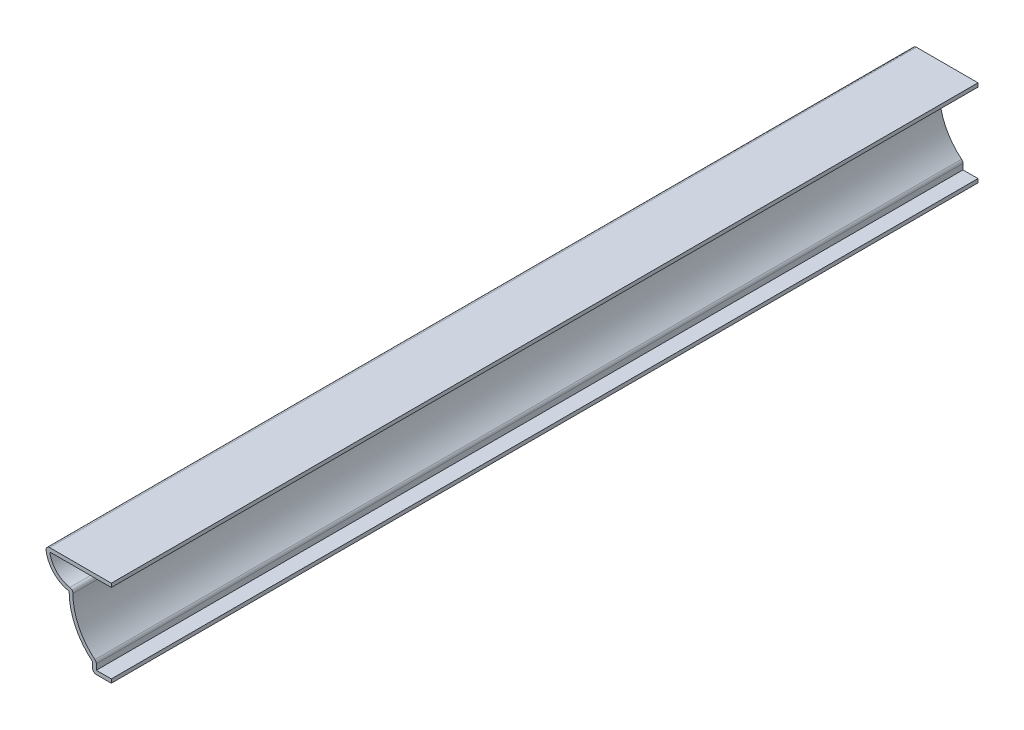
SolidWorks part; units mm, degrees
ref_plane "Front Plane" through (0, 0, 0) normal (0, 0, 1) x (1, 0, 0)
ref_plane "Top Plane" through (0, 0, 0) normal (0, 1, 0) x (1, 0, 0)
ref_plane "Right Plane" through (0, 0, 0) normal (1, 0, 0) x (0, 0, -1)
sketch "Sketch1" plane through (0, 0, 0) normal (0, 0, 1) x (1, 0, 0)
  line L0 (0, 0) -> (0, 22.7012) construction
  line L1 (0, 0) -> (-6.35, 0)
  line L2 (-6.35, 0) -> (-6.35, 3.175)
  line L3 (-22.225, 29.3687) -> (0, 29.3687)
  arc A0 (-6.35, 3.175) -> (-14.2875, 19.8437) centre (7.1834, 19.8438) cw
  arc A1 (-14.2875, 19.8437) -> (-22.225, 29.3687) centre (-12.5412, 29.3687) cw
  point P9 (0, 0)
  point P11 (-17.312, 23.5135)
  point P12 (0, 21.1484)
  dimension "D1" = 6.35
  dimension "D2" = 3.175
  dimension "D4" = 7.9375
  dimension "D5" = 7.9375
  dimension "D6" = 9.525
  dimension "D7" = 22.225
  dimension "D8" = 29.3687
extrude "Extrude-Thin1" add sketch "Sketch1" against normal blind 293.6875 thin
fillet "Fillet1" radius 1.27 4 edges at (-6.35, 0, -146.8438) (-5.08, 3.7911, -146.8438) (-12.9863, 20.9668, -146.8438) (-22.225, 29.3687, -146.8438)
